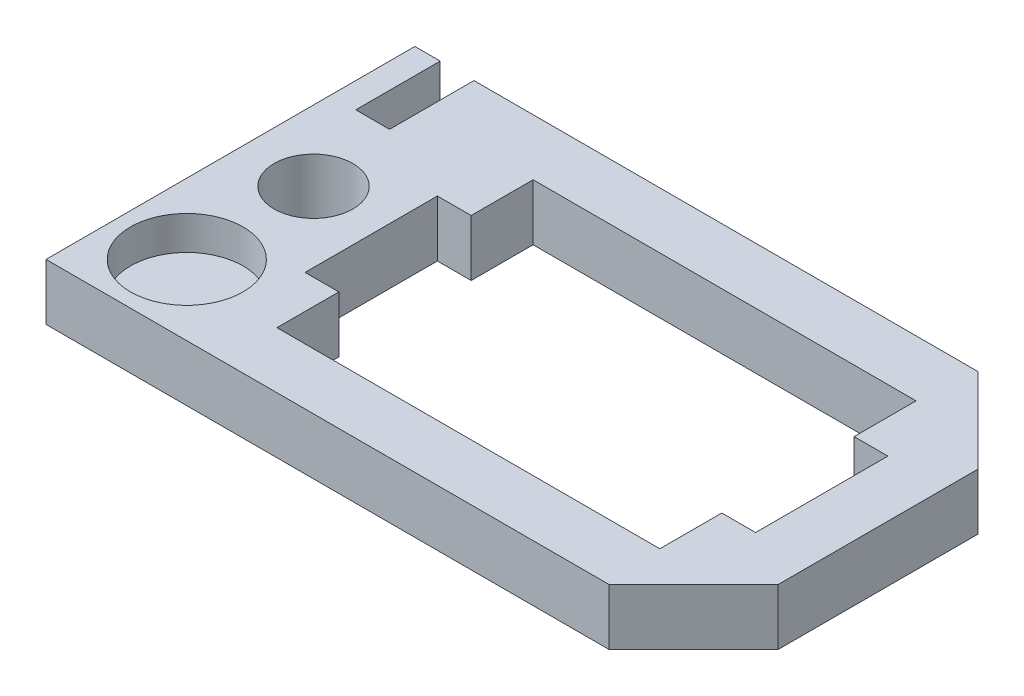
SolidWorks part; units mm, degrees
ref_plane "Plan de face" through (0, 0, 0) normal (0, 0, 1) x (1, 0, 0)
ref_plane "Plan de dessus" through (0, 0, 0) normal (0, 1, 0) x (1, 0, 0)
ref_plane "Plan de droite" through (0, 0, 0) normal (1, 0, 0) x (0, 0, -1)
sketch "Esquisse1" plane through (0, 0, 0) normal (0, 1, 0) x (1, 0, 0)
  line L1 (0, 0) -> (23, 0)
  line L3 (0, 13.1) -> (23, 13.1)
  line L4 (23, 0) -> (23, 13.1)
  line L5 (6.2, 11.1) -> (19.8, 11.1)
  line L6 (6.2, 11.1) -> (6.2, 2)
  line L7 (6.2, 2) -> (19.8, 2)
  line L8 (19.8, 11.1) -> (19.8, 2)
  line L9 (6.2, 11.1) -> (19.8, 2) construction
  line L10 (13, 11.1) -> (13, 2) construction
  line L11 (19.8, 8.9) -> (21, 8.9)
  line L12 (19.8, 8.9) -> (19.8, 4.2)
  line L13 (19.8, 4.2) -> (21, 4.2)
  line L14 (21, 8.9) -> (21, 4.2)
  line L15 (5, 8.9) -> (5, 4.2)
  line L16 (6.2, 4.2) -> (5, 4.2)
  line L17 (6.2, 8.9) -> (6.2, 4.2)
  line L18 (6.2, 8.9) -> (5, 8.9)
  line L19 (0, 13.1) -> (0, 0)
  point P15 (19.8, 6.55)
  point P16 (19.8, 6.55)
  dimension "D1" = 13.6
  dimension "D2" = 9.1
  dimension "D3" = 1.2
  dimension "D4" = 4.7
  dimension "D5" = 2
  dimension "D6" = 2
  dimension "D7" = 5
  dimension "D8" = 2
extrude "Boss.-Extru.1" add sketch "Esquisse1" along normal blind 2
sketch "Esquisse2" plane through (0, 2, 0) normal (0, 1, 0) x (1, 0, 0)
  line L0 (0, 13.1) -> (0, 0) construction
  line L4 (0, 0) -> (23, 0) construction
  circle A0 centre (2.5, 7) radius 1.4
  dimension "D1" = 2.8
  dimension "D3" = 7
  dimension "D2" = 2.5
extrude "Enlèv. mat.-Extru.4" cut sketch "Esquisse2" against normal up to next
chamfer "Chanfrein1" distance 3 angle 45 2 edges at (23, 1, -13.1) (23, 1, 0)
sketch "Esquisse3" plane through (0, 0, -13.1) normal (0, 0, -1) x (-1, 0, 0)
  line L0 (0, 2) -> (-20, 2) construction
  line L1 (-0.9, 2) -> (-2.1, 2)
  line L2 (-0.9, 2) -> (-0.9, 0)
  line L3 (-0.9, 0) -> (-2.1, 0)
  line L4 (-2.1, 2) -> (-2.1, 0)
  line L5 (0, 0) -> (-20, 0) construction
  line L6 (0, 2) -> (0, 0) construction
  dimension "D1" = 1.2
  dimension "D2" = 0.9
extrude "Enlèv. mat.-Extru.5" cut sketch "Esquisse3" against normal blind 3
sketch "Esquisse4" plane through (0, 2, 0) normal (0, 1, 0) x (1, 0, 0)
  line L0 (0, 0) -> (20, 0) construction
  line L1 (0, 13.1) -> (0, 0) construction
  circle A0 centre (2.5, 2.5) radius 2
  dimension "D1" = 4
  dimension "D2" = 2.5
  dimension "D3" = 2.5
extrude "Enlèv. mat.-Extru.6" cut sketch "Esquisse4" against normal blind 1.2
